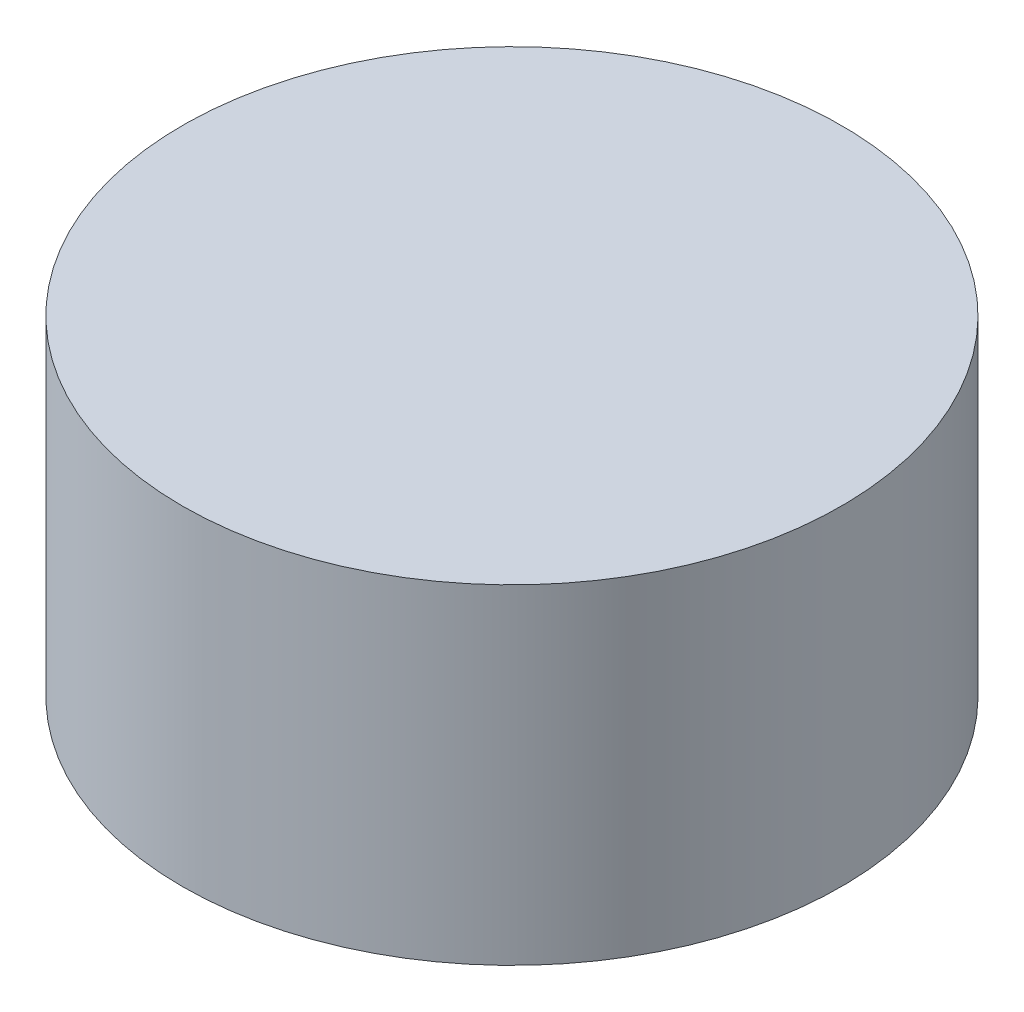
SolidWorks part; units mm, degrees
material "ABS"
ref_plane "Front Plane" through (0, 0, 0) normal (0, 0, 1) x (1, 0, 0)
ref_plane "Top Plane" through (0, 0, 0) normal (0, 1, 0) x (1, 0, 0)
ref_plane "Right Plane" through (0, 0, 0) normal (1, 0, 0) x (0, 0, -1)
sketch "Sketch1" plane through (0, 0, 0) normal (0, 1, 0) x (1, 0, 0)
  circle A0 centre (0, 0) radius 2
  dimension "D1" = 4
extrude "Base" add sketch "Sketch1" along normal blind 2
